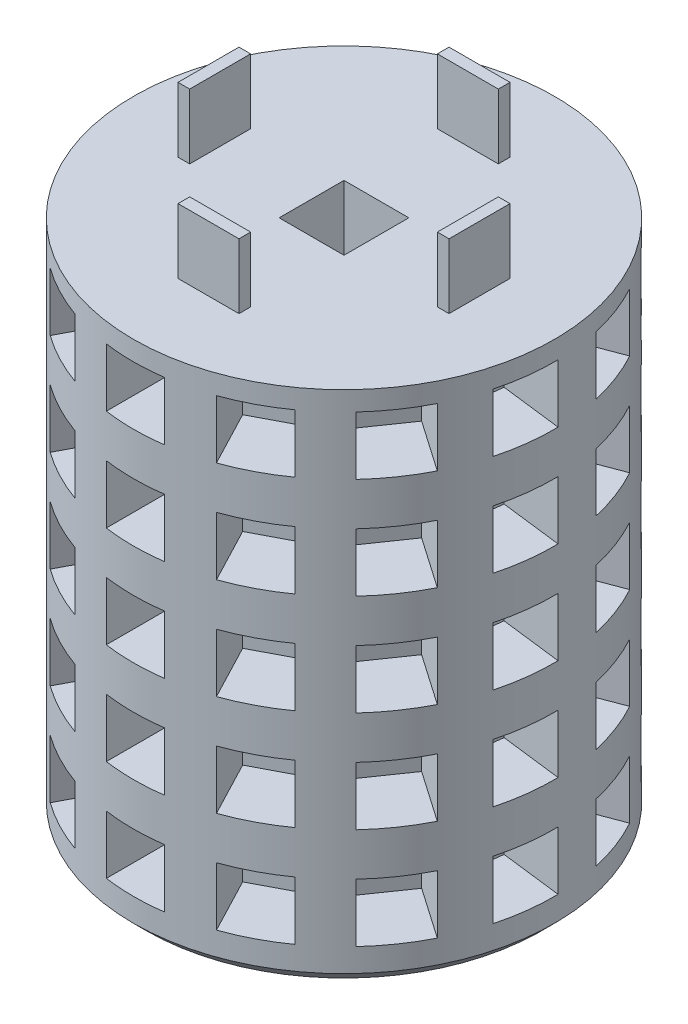
SolidWorks part; units mm, degrees
ref_plane "Front Plane" through (0, 0, 0) normal (0, 0, 1) x (1, 0, 0)
ref_plane "Top Plane" through (0, 0, 0) normal (0, 1, 0) x (1, 0, 0)
ref_plane "Right Plane" through (0, 0, 0) normal (1, 0, 0) x (0, 0, -1)
sketch "Sketch1" plane through (0, 0, 0) normal (0, 1, 0) x (1, 0, 0)
  circle A0 centre (0, 0) radius 41.2369
  dimension "D1" = 82.4738
extrude "Boss-Extrude1" add sketch "Sketch1" along normal blind 203.2 contours A0
sketch "Sketch2" plane through (0, 0, 0) normal (0, -1, 0) x (-1, 0, 0)
  line L3 (0, -6.35) -> (6.35, -6.35)
  line L5 (0, 6.35) -> (6.35, 6.35)
  line L6 (6.35, -6.35) -> (6.35, 6.35)
  line L7 (0, -6.35) -> (-6.35, -6.35)
  line L9 (0, 6.35) -> (-6.35, 6.35)
  line L10 (-6.35, -6.35) -> (-6.35, 6.35)
extrude "Cut-Extrude1" cut sketch "Sketch2" against normal through all contours L10 L9 L5 L6 L3 L7
ref_plane "Plane2" through (0, 0, 60.96) normal (0, 0, 1) x (1, 0, 0)
chamfer "Chamfer1" distance 2.54 angle 45 1 edges at (0, 203.2, 41.2369)
chamfer "Chamfer2" distance 2.54 angle 45 1 edges at (0, 0, 41.2369)
ref_plane "Plane3" through (0, 0, 48.26) normal (0, 0, 1) x (1, 0, 0)
ref_plane "Plane4" through (0, 0, 41.402) normal (0, 0, 1) x (1, 0, 0)
sketch "Sketch3" plane through (0, 0, 41.402) normal (0, 0, 1) x (1, 0, 0)
  line L0 (-41.2369, 200.66) -> (41.2369, 200.66) construction
  line L1 (0, 200.66) -> (-9.525, 200.66)
  line L2 (-9.525, 200.66) -> (9.525, 181.61)
  line L3 (-3.81, 181.61) -> (-9.525, 181.61)
  line L4 (-9.525, 200.66) -> (-9.525, 181.61)
  line L5 (-9.525, 181.61) -> (9.525, 200.66)
  line L6 (0, 200.66) -> (9.525, 200.66)
  line L8 (-3.81, 181.61) -> (9.525, 181.61)
  line L9 (9.525, 200.66) -> (9.525, 181.61)
sketch "Sketch6" plane through (0, 0, 41.402) normal (0, 0, 1) x (1, 0, 0)
  line L0 (-9.525, 181.61) -> (9.525, 200.66) construction
  line L3 (0, 196.85) -> (5.715, 196.85)
  line L4 (5.715, 191.135) -> (5.715, 196.85)
  line L5 (-9.525, 200.66) -> (9.525, 181.61) construction
  line L8 (0, 196.85) -> (-5.715, 196.85)
  line L9 (-5.715, 191.135) -> (-5.715, 196.85)
  line L12 (-5.715, 191.135) -> (-5.715, 185.42)
  line L13 (-5.715, 185.42) -> (5.715, 185.42)
  line L14 (5.715, 191.135) -> (5.715, 185.42)
extrude "Cut-Extrude3" cut sketch "Sketch6" against normal blind 12.7 contours L3 L4 L14 L13 L12 L9 L8
pattern_linear "LPattern1" count 10 spacing 19.812 along (0, -1, 0) of "Cut-Extrude3"
pattern_circular "CirPattern1" count 13 every 27.7 about axis through (0, 0, 0) along (0, 1, 0) of "LPattern1", "Cut-Extrude3"
sketch "Sketch7" plane through (0, 203.2, 0) normal (0, 1, 0) x (1, 0, 0)
  circle A0 centre (0, 0) radius 41.2369
extrude "Cut-Extrude4" cut sketch "Sketch7" against normal blind 101.6 contours A0
sketch "Sketch8" plane through (0, 101.6, 0) normal (0, 1, 0) x (1, 0, 0)
  line L2 (6.35, -6.35) -> (6.35, 6.35) construction
  line L3 (24.257, -5.969) -> (26.543, -5.969)
  line L4 (6.35, 6.35) -> (-6.35, 6.35) construction
  line L5 (24.257, -5.969) -> (24.257, 5.969)
  line L6 (24.257, 5.969) -> (26.543, 5.969)
  line L7 (26.543, -5.969) -> (26.543, 5.969)
  line L8 (24.257, -5.969) -> (26.543, 5.969) construction
  line L9 (24.257, 5.969) -> (26.543, -5.969) construction
  line L10 (-5.969, 26.543) -> (5.969, 26.543)
  line L11 (-5.969, 26.543) -> (-5.969, 24.257)
  line L12 (6.35, -6.35) -> (-6.35, -6.35) construction
  line L13 (-5.969, 24.257) -> (5.969, 24.257)
  line L14 (5.969, 26.543) -> (5.969, 24.257)
  line L15 (-5.969, -26.543) -> (5.969, -26.543)
  line L16 (-5.969, 26.543) -> (5.969, 24.257) construction
  line L17 (-5.969, 24.257) -> (5.969, 26.543) construction
  line L18 (-5.969, -26.543) -> (-5.969, -24.257)
  line L19 (-5.969, -24.257) -> (5.969, -24.257)
  line L20 (5.969, -26.543) -> (5.969, -24.257)
  line L21 (-5.969, -26.543) -> (5.969, -24.257) construction
  line L22 (-5.969, -24.257) -> (5.969, -26.543) construction
  line L23 (-6.35, -6.35) -> (-6.35, 6.35) construction
  line L24 (-26.543, -5.969) -> (-24.257, -5.969)
  line L25 (-26.543, -5.969) -> (-26.543, 5.969)
  line L26 (-26.543, 5.969) -> (-24.257, 5.969)
  line L27 (-24.257, -5.969) -> (-24.257, 5.969)
  line L28 (-26.543, -5.969) -> (-24.257, 5.969) construction
  line L29 (-26.543, 5.969) -> (-24.257, -5.969) construction
  point P0 (25.4, 0)
  point P11 (0, -25.4)
  point P16 (0, 25.4)
  point P24 (-25.4, 0)
  dimension "D1" = 19.05
  dimension "D2" = 2.286
  dimension "D3" = 11.938
  dimension "D4" = 19.05
  dimension "D5" = 11.938
  dimension "D6" = 2.286
  dimension "D7" = 11.938
  dimension "D8" = 19.05
  dimension "D9" = 2.286
  dimension "D10" = 19.05
  dimension "D11" = 2.286
  dimension "D12" = 11.938
extrude "Boss-Extrude2" add sketch "Sketch8" along normal blind 12.7
